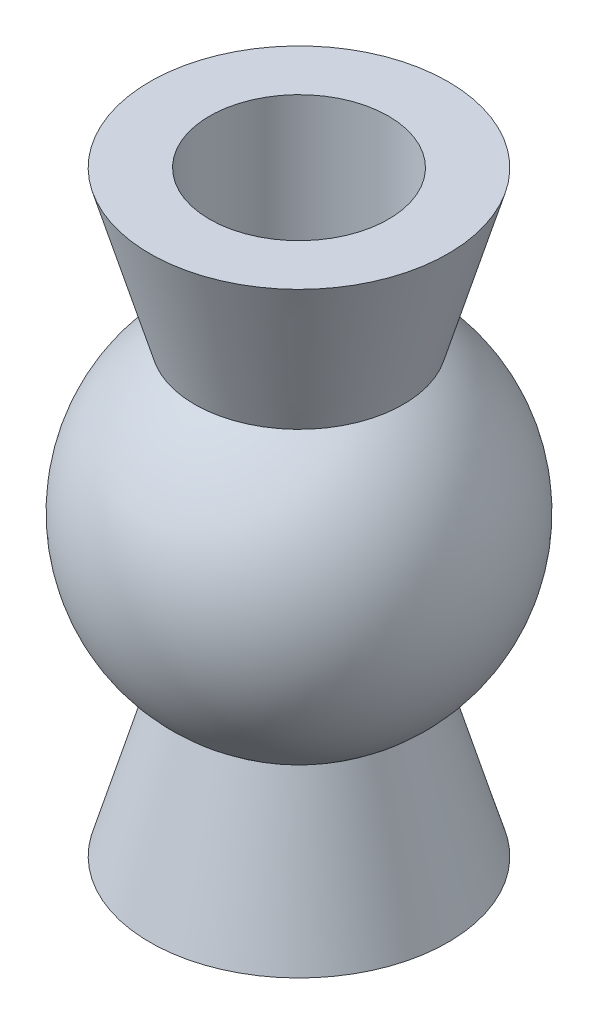
SolidWorks part; units mm, degrees
material "Chrome Stainless Steel"
ref_plane "Front Plane" through (0, 0, 0) normal (0, 0, 1) x (1, 0, 0)
ref_plane "Top Plane" through (0, 0, 0) normal (0, 1, 0) x (1, 0, 0)
ref_plane "Right Plane" through (0, 0, 0) normal (1, 0, 0) x (0, 0, -1)
sketch "Sketch1" plane through (0, 0, 0) normal (0, 0, 1) x (1, 0, 0)
  line L0 (2.5, 0) -> (1.5, 0)
  line L1 (2.5, 0) -> (1.75, 2.5633)
  line L2 (0, 0) -> (0, 27.8427) construction
  line L3 (1.75, 7.4367) -> (2.5, 10)
  line L4 (1.5, 0) -> (1.5, 10)
  line L5 (1.5, 10) -> (2.5, 10)
  arc A0 (1.75, 2.5633) -> (1.75, 7.4367) centre (0, 5) ccw
  dimension "D1" = 3
  dimension "D2" = 5
  dimension "D3" = 3
  dimension "D4" = 10
  dimension "D5" = 3.5
revolve "Revolve1" add sketch "Sketch1" angle 360 about L2
